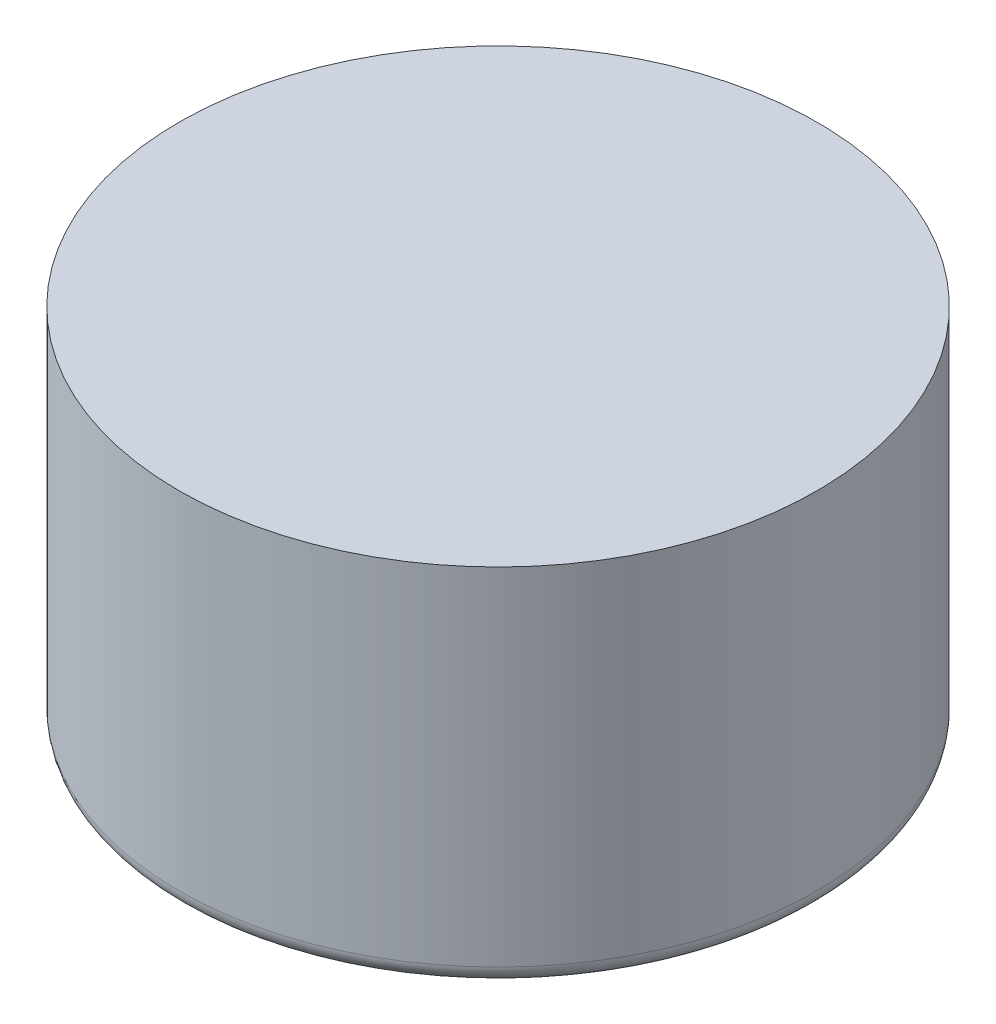
SolidWorks part; units mm, degrees
ref_plane "Front Plane" through (0, 0, 0) normal (0, 0, 1) x (1, 0, 0)
ref_plane "Top Plane" through (0, 0, 0) normal (0, 1, 0) x (1, 0, 0)
ref_plane "Right Plane" through (0, 0, 0) normal (1, 0, 0) x (0, 0, -1)
sketch "Sketch1" plane through (0, 0, 0) normal (0, 1, 0) x (1, 0, 0)
  circle A0 centre (0, 0) radius 1.75
  dimension "D1" = 3.5
extrude "Boss-Extrude1" add sketch "Sketch1" along normal blind 2
fillet "Fillet3" radius 0.1 1 edges at (0, 0, 1.75)
